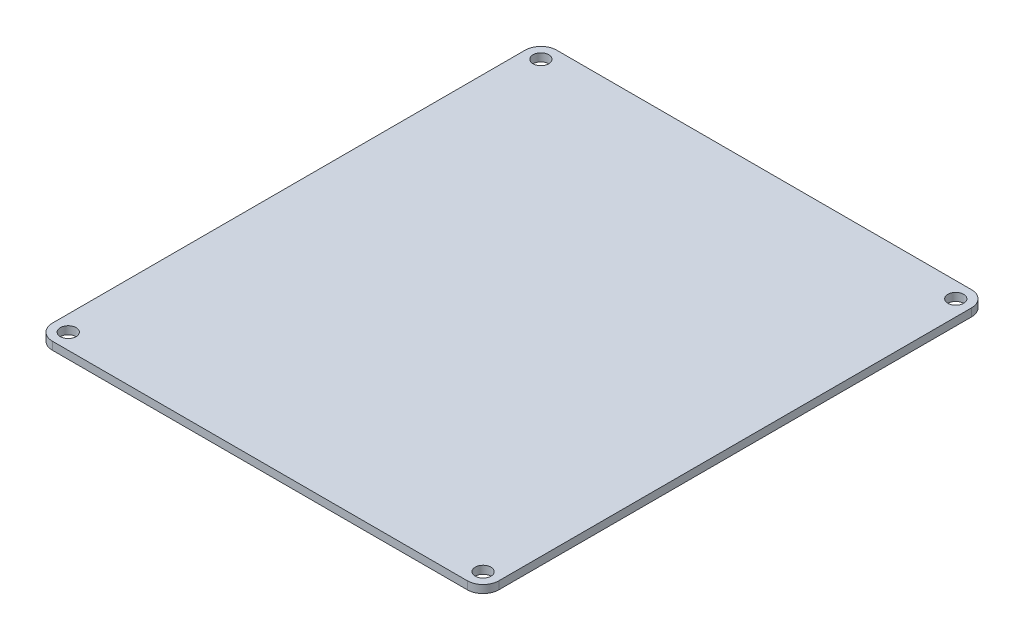
SolidWorks part; units mm, degrees
material "Delrin 2700 NC010, Low Viscosity Acetal Copolymer (SS)"
ref_plane "Front" through (0, 0, 0) normal (0, 0, 1) x (1, 0, 0)
ref_plane "Top" through (0, 0, 0) normal (0, 1, 0) x (1, 0, 0)
ref_plane "Right" through (0, 0, 0) normal (1, 0, 0) x (0, 0, -1)
sketch "Sketch1" plane through (0, 0, 0) normal (0, 1, 0) x (1, 0, 0)
  line B0 (-32.8, 203.2) -> (-32.8, 0)
  line B1 (147.1, 0) -> (147.1, 203.2)
  line B2 (147.1, 203.2) -> (-147.1, 203.2)
  line B3 (-147.1, 203.2) -> (-147.1, 0)
  line B4 (-147.1, 0) -> (147.1, 0)
  circle B5 centre (140.75, 196.85) radius 3.175
  circle B6 centre (140.75, 6.35) radius 3.175
  circle B7 centre (-26.45, 196.85) radius 3.175
  circle B8 centre (-26.45, 6.35) radius 3.175
sketch_block_instance "Block-ElectronicsMounting-1"
sketch_block "Block-ElectronicsMounting"
extrude "Boss-Extrude1" add sketch "Sketch1" along normal blind 3.175 contours B0 B4 B1 B2 B8 B7 B6 B5
fillet "Fillet1" radius 6.35 4 edges at (147.1, 1.5875, 0) (-32.8, 1.5875, 0) (-32.8, 1.5875, -203.2) (147.1, 1.5875, -203.2)
